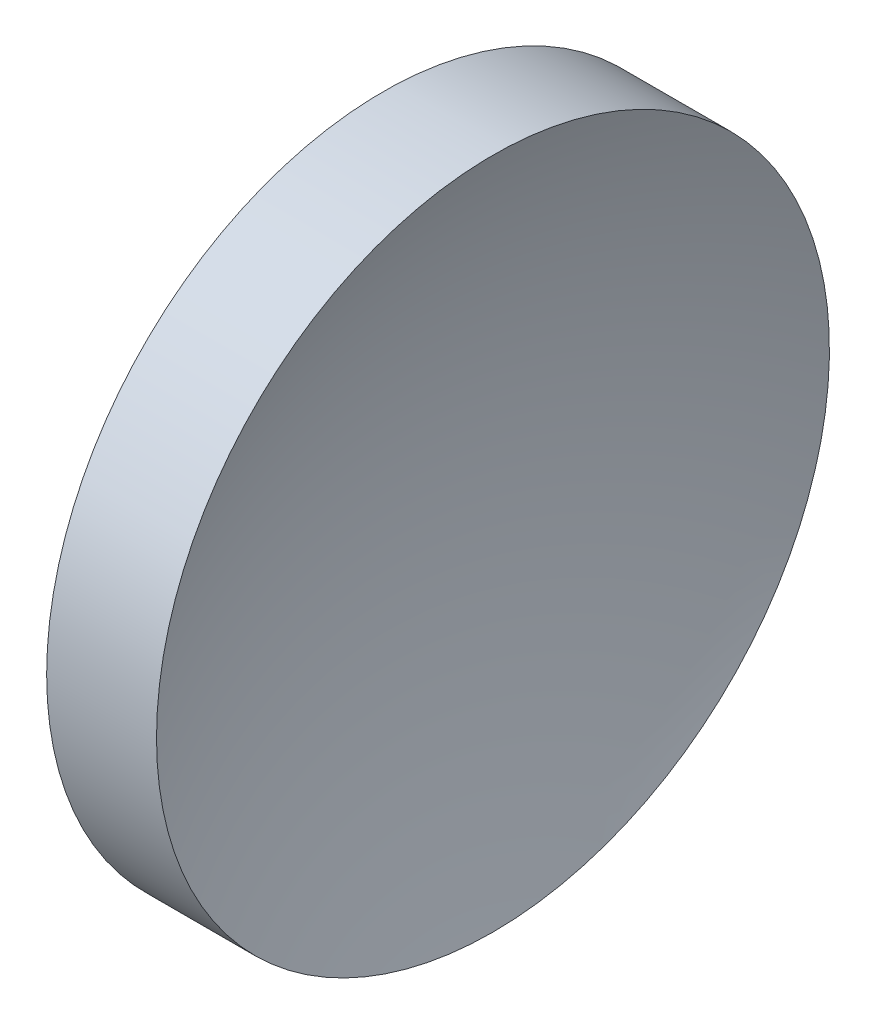
SolidWorks part; units mm, degrees
ref_plane "前视基准面" through (0, 0, 0) normal (0, 0, 1) x (1, 0, 0)
ref_plane "上视基准面" through (0, 0, 0) normal (0, 1, 0) x (1, 0, 0)
ref_plane "右视基准面" through (0, 0, 0) normal (1, 0, 0) x (0, 0, -1)
sketch "草图1" plane through (0, 0, 0) normal (0, 0, 1) x (1, 0, 0)
  line L0 (105.6218, 65.1556) -> (137.1869, 65.1556) construction
  line L1 (113.9119, 65.1556) -> (113.9119, 85.1556)
  line L2 (113.9119, 85.1556) -> (120.4422, 85.1556)
  line L3 (116.4119, 65.1556) -> (113.9119, 65.1556)
  arc A0 (120.4422, 85.1556) -> (116.4119, 65.1556) centre (168.0519, 65.1556) ccw
revolve "旋转1" add sketch "草图1" angle 360 about L0
